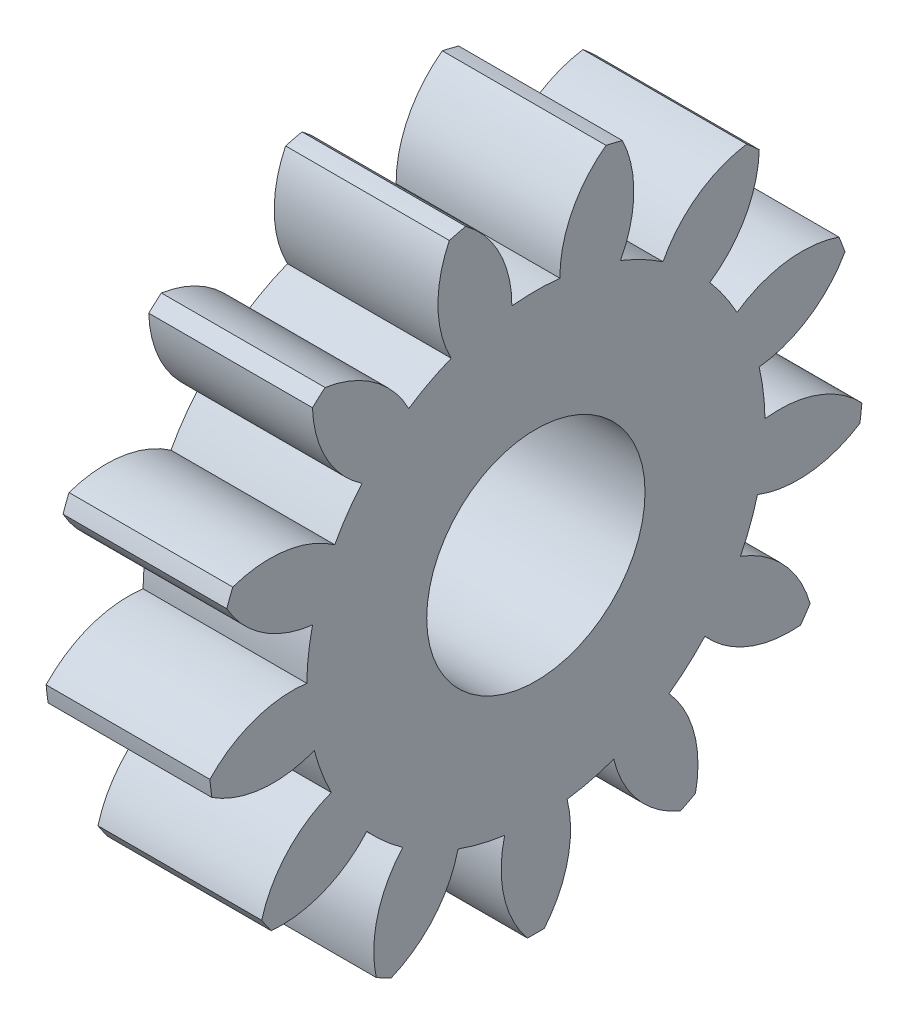
SolidWorks part; units mm, degrees
ref_plane "Plane1" through (0, 0, 0) normal (0, 0, 1) x (1, 0, 0)
ref_plane "Plane2" through (0, 0, 0) normal (0, 1, 0) x (1, 0, 0)
ref_plane "Plane3" through (0, 0, 0) normal (1, 0, 0) x (0, 0, -1)
sketch "HoldingSke" plane through (0, 0, 0) normal (0, 1, 0) x (1, 0, 0)
  line L0 (0, 0) -> (2.4359, -0.5624)
  line L1 (-15, 0) -> (100, 0) construction
  line L2 (0, 0) -> (-2.1039, 2.3779)
  line L3 (0, 0) -> (-11.863, 4.5341)
  line L4 (0, 0) -> (8.4147, 1.9427)
  line L5 (0, 0) -> (-46.8476, -17.4728)
  line L6 (0, 0) -> (-1.2434, -0.839)
  line L7 (-2.1039, 2.3779) -> (8.6586, 51.2059)
  line L8 (-76.2, 54.61) -> (-75.9, 54.61)
  line L9 (-71.009, 38.7566) -> (-53.1078, 45.2721)
  line L10 (-76.2, 71.12) -> (104.1128, 71.12)
  line L11 (0, 0) -> (-1.5, 0)
  line L12 (-76.2, 101.6) -> (-76.185, 101.6)
  line L13 (24.9733, 27.94) -> (52.9518, 28.4284)
  line L14 (24.9733, 27.94) -> (24.9743, 27.94)
  line L15 (24.9733, 27.94) -> (100.4006, 29.5858)
  line L16 (-63.627, -0.4) -> (-12.827, -0.4)
  circle A0 centre (0, 0) radius 1
  circle A1 centre (0, 0) radius 2.099
  circle A2 centre (0, 0) radius 37.5
  circle A3 centre (0, 0) radius 1
  dimension "MHD" = 4.198
  dimension "Hub_dia" = 75
  dimension "Bore" = 2
  dimension "MBD" = 2
  dimension "Num_teeth" = 13
  dimension "Pitch" = 2.5
  dimension "Overall_len" = 50
  dimension "Show_teeth" = 13
  dimension "Thickness" = 1.5
  dimension "OAL" = 50.0001
  dimension "T_dim" = 0.3
  dimension "Ap" = 20
  dimension "H" = 19.05
  dimension "Pitch_radius" = 180.3128
  dimension "Width" = 1.5
  dimension "Backlash" = 0.015
  dimension "Addendum_fac" = 1
  dimension "Dedendum_fac" = 1.25
  dimension "Clearance_fac" = 0.25
  dimension "Dedendum_add" = 0.001
  dimension "Module" = 0.4
sketch "BasProSke" plane through (0, 0, 0) normal (0, 1, 0) x (1, 0, 0)
  line L0 (-10, 0) -> (60, 0) construction
  line L1 (0, 0) -> (0, 3)
  line L2 (0, 0) -> (1.5, 0)
  line L3 (1.5, 0) -> (1.5, 3)
  line L4 (1.5, 3) -> (0, 3)
  dimension "Thickness" = 1.5
  dimension "Diameter" = 6
revolve "Base-Revolve" add sketch "BasProSke" angle 360 about L0
sketch "TooCutSke" plane through (0, 0, 0) normal (1, 0, 0) x (0, 0, -1)
  line L1 (0, 0) -> (0, 107) construction
  line L2 (0, 0) -> (-0.3396, 2.5777) construction
  line L3 (0, 0) -> (-1.2368, 5.018) construction
  line L4 (-0.3396, 2.5777) -> (-0.6184, 2.509) construction
  arc A0 (0.2199, 2.0874) -> (-0.2199, 2.0874) centre (0, 0) ccw
  arc A1 (0.6705, 2.9502) -> (-0.6705, 2.9502) centre (0, 0) ccw
  circle A2 centre (0, 0) radius 2.6 construction
  circle A3 centre (0, 0) radius 2.4432 construction
  arc A4 (-0.2199, 2.0874) -> (-0.6705, 2.9502) centre (-1.2599, 2.0933) ccw
  arc A5 (0.6705, 2.9502) -> (0.2199, 2.0874) centre (1.2599, 2.0933) ccw
  dimension "Root_dia" = 4.198
  dimension "Overcut_dia" = 6.0508
  dimension "Pitch_dia" = 5.2
  dimension "Base_dia" = 4.8864
  dimension "Flank_rad" = 1.04
  dimension "Half_ang" = 13.846
  dimension "Half_CT" = 0.2871
extrude "ToothCut" cut sketch "TooCutSke" along normal through all
fillet "Breaks" [suppressed] radius 0.008
fillet "RootFillets" [suppressed] radius 0.101
pattern_circular "TeethCuts" count 13 every 27.692 about axis through (-10, 0, 0) along (1, 0, 0) of "ToothCut", "RootFillets", "Breaks"
sketch "HubNeaOneSke" plane through (0, 0, 0) normal (-1, 0, 0) x (0, 0, 1)
  circle A0 centre (0, 0) radius 2.099
  dimension "Diameter" = 4.198
extrude "HubNearOne" [suppressed] add sketch "HubNeaOneSke" along normal blind 48.5001
sketch "HubNeaBotSke" plane through (0, 0, 0) normal (-1, 0, 0) x (0, 0, 1)
  circle A0 centre (0, 0) radius 2.099
  dimension "Diameter" = 4.198
extrude "HubNearBoth" [suppressed] add sketch "HubNeaBotSke" along normal blind 24.25
ref_plane "FarPln" through (1.5, 0, 0) normal (1, 0, 0) x (0, 0, -1)
sketch "HubFarSke" plane through (1.5, 0, 0) normal (1, 0, 0) x (0, 0, -1)
  circle A0 centre (0, 0) radius 2.099
  dimension "Diameter" = 4.198
extrude "HubFar" [suppressed] add sketch "HubFarSke" along normal blind 24.25
sketch "BorSke" plane through (0, 0, 0) normal (1, 0, 0) x (0, 0, -1)
  circle A0 centre (0, 0) radius 1
  dimension "Diameter" = 2
extrude "Bore" cut sketch "BorSke" along normal mid plane 100.0001
sketch "KeySke" plane through (0, 0, 0) normal (1, 0, 0) x (0, 0, -1)
  line L0 (-0.4, 0) -> (-0.4, 1.3)
  line L1 (-0.4, 1.3) -> (0.4, 1.3)
  line L2 (0.4, 1.3) -> (0.4, 0)
  line L3 (0, 0) -> (0, 34) construction
  line L4 (-0.4, 0) -> (0.4, 0)
  dimension "Offset" = 1.3
  dimension "Width" = 0.8
extrude "Keyway" [suppressed] cut sketch "KeySke" along normal mid plane 100.0001
pattern_circular "Keyway2" [suppressed] count 2 every 90 about axis through (-10, 0, 0) along (1, 0, 0)
equation "' \"Module@HoldingSke\" = 6.35"
equation "' \"Num_teeth@HoldingSke\" = 12"
equation "' \"Ap@HoldingSke\" =  20"
equation "' \"Ap@HoldingSke\" = 20"
equation "' \"Width@HoldingSke\" = 0.5 * 25.4"
equation "' \"Hub_dia@HoldingSke\"= 1 * 25.4"
equation "' \"Hub_dia@HoldingSke\" = 1 * 25.4"
equation "' \"Overall_len@HoldingSke\" = 1.0 * 25.4"
equation "' \"Bore@HoldingSke\" = 0.75 * 25.4"
equation "' \"T_dim@HoldingSke\" = 0.1 * 25.4"
equation "' \"Width@KeySke\" = 0.25 * 25.4"
equation "' \"Show_teeth@HoldingSke\" = 13"
equation "' \"Backlash@HoldingSke\" = 0.009 * 25.4"
equation "' \"Addendum_fac@HoldingSke\" = 1.0"
equation "' \"Dedendum_fac@HoldingSke\" = 1.25"
equation "' \"Dedendum_add@HoldingSke\" = 0.00005 * 25.4"
equation "' \"Clearance_fac@HoldingSke\" = 0.25"
equation "\"Pitch@HoldingSke\" = 1 / \"Module@HoldingSke\""
equation "\"Overcut_dia@TooCutSke\" = (\"Num_teeth@HoldingSke\" + 2 * \"Addendum_fac@HoldingSke\") / \"Pitch@HoldingSke\" + 0.002 * 25.4"
equation "\"Pitch_dia@TooCutSke\" = \"Num_teeth@HoldingSke\" / \"Pitch@HoldingSke\""
equation "\"Base_dia@TooCutSke\" = \"Num_teeth@HoldingSke\" / \"Pitch@HoldingSke\" * cos((\"Ap@HoldingSke\"  * 3.14159265 / 180))"
equation "\"Root_dia@TooCutSke\" = (\"Num_teeth@HoldingSke\" + 2) / \"Pitch@HoldingSke\" - 2 * (\"Addendum_fac@HoldingSke\" + \"Dedendum_fac@HoldingSke\") / \"Pitch@HoldingSke\" - \"Dedendum_add@HoldingSke\" * 2"
equation "\"Half_ang@TooCutSke\" = 180 / \"Num_teeth@HoldingSke\""
equation "\"Half_CT@TooCutSke\" = \"Num_teeth@HoldingSke\" / \"Pitch@HoldingSke\" * sin((3.14159265 / 2 / \"Num_teeth@HoldingSke\")) / 2 - 7 * \"Backlash@HoldingSke\" / 4"
equation "\"Flank_rad@TooCutSke\" = \"Num_teeth@HoldingSke\" / \"Pitch@HoldingSke\" / 5"
equation "\"Radius@RootFillets\" = \"Clearance_fac@HoldingSke\" / \"Pitch@HoldingSke\" + \"Dedendum_add@HoldingSke\""
equation "\"Break_rad@Breaks\" = 0.02 / \"Pitch@HoldingSke\""
equation "\"Thickness@HoldingSke\" = \"Width@HoldingSke\""
equation "\"OAL@HoldingSke\" = \"Thickness@HoldingSke\""
equation "\"MHD@HoldingSke\" = (\"Num_teeth@HoldingSke\" + 2) / \"Pitch@HoldingSke\" - 2 * (\"Addendum_fac@HoldingSke\" + \"Dedendum_fac@HoldingSke\")  / \"Pitch@HoldingSke\" - \"Dedendum_add@HoldingSke\" * 2"
equation "\"MBD@HoldingSke\" = (\"Num_teeth@HoldingSke\" + 2) / \"Pitch@HoldingSke\" - 2 * (\"Addendum_fac@HoldingSke\" + \"Dedendum_fac@HoldingSke\")  / \"Pitch@HoldingSke\" - \"Dedendum_add@HoldingSke\" * 2 - 0.002 * 25.4"
equation "\"MHD@HoldingSke\" = ((sgn( \"MHD@HoldingSke\" - \"Hub_dia@HoldingSke\" )-1)*( \"MHD@HoldingSke\" - \"Hub_dia@HoldingSke\" ))/-2+ \"Hub_dia@HoldingSke\""
equation "\"MBD@HoldingSke\" = ((sgn( \"MBD@HoldingSke\" - \"Bore@HoldingSke\" )-1)*( \"MBD@HoldingSke\" - \"Bore@HoldingSke\" ))/-2+ \"Bore@HoldingSke\""
equation "\"OAL@HoldingSke\" = ((sgn( \"OAL@HoldingSke\" - \"Overall_len@HoldingSke\" )+1)*( \"OAL@HoldingSke\" - \"Overall_len@HoldingSke\" ))/2 + \"Overall_len@HoldingSke\" + 0.000002 * 25.4"
equation "\"Num_teeth@TeethCuts\" = int( \"Show_teeth@HoldingSke\" ) + 1"
equation "\"Num_teeth@TeethCuts\" = ((sgn( \"Num_teeth@TeethCuts\" - \"Num_teeth@HoldingSke\" )-1)*( \"Num_teeth@TeethCuts\" - \"Num_teeth@HoldingSke\" ))/-2+ \"Num_teeth@HoldingSke\""
equation "\"Num_teeth@TeethCuts\" = ((sgn( \"Num_teeth@TeethCuts\" - 2.0)+1)*( \"Num_teeth@TeethCuts\" - 2.0))/2 +2.0"
equation "\"Angle@TeethCuts\" = 360.0 / \"Num_teeth@HoldingSke\""
equation "\"Diameter@BasProSke\" = (\"Num_teeth@HoldingSke\" + 2 * \"Addendum_fac@HoldingSke\") / \"Pitch@HoldingSke\""
equation "\"Thickness@BasProSke\"  = \"Thickness@HoldingSke\""
equation "' \"Fillet_rad@BasProSke\" =  \"Thickness@HoldingSke\" * 0.05"
equation "' \"Fillet_rad@BasProSke\" = \"Thickness@HoldingSke\" * 0.05"
equation "\"MHD@HoldingSke\" = ((sgn( \"MHD@HoldingSke\" - \"Root_dia@TooCutSke\" )-1)*( \"MHD@HoldingSke\" - \"Root_dia@TooCutSke\" ))/-2+ \"Root_dia@TooCutSke\""
equation "\"Diameter@HubNeaOneSke\" = \"MHD@HoldingSke\""
equation "\"Length@HubNearOne\" = \"OAL@HoldingSke\" - \"Thickness@BasProSke\""
equation "\"Diameter@HubNeaBotSke\" = \"MHD@HoldingSke\""
equation "\"Length@HubNearBoth\" = ( \"OAL@HoldingSke\" - \"Thickness@BasProSke\" ) / 2.0"
equation "\"Thickness@FarPln\" = \"Thickness@BasProSke\""
equation "\"Diameter@HubFarSke\" = \"MHD@HoldingSke\""
equation "\"Length@HubFar\" = ( \"OAL@HoldingSke\" - \"Thickness@BasProSke\" ) / 2.0"
equation "\"Diameter@BorSke\" = \"MBD@HoldingSke\""
equation "\"D1@Bore\" = \"OAL@HoldingSke\" * 2.0"
equation "\"D1@Keyway\" = \"OAL@HoldingSke\" * 2.0"
equation "\"Offset@KeySke\" = \"T_dim@HoldingSke\" + \"MBD@HoldingSke\" / 2.0"
